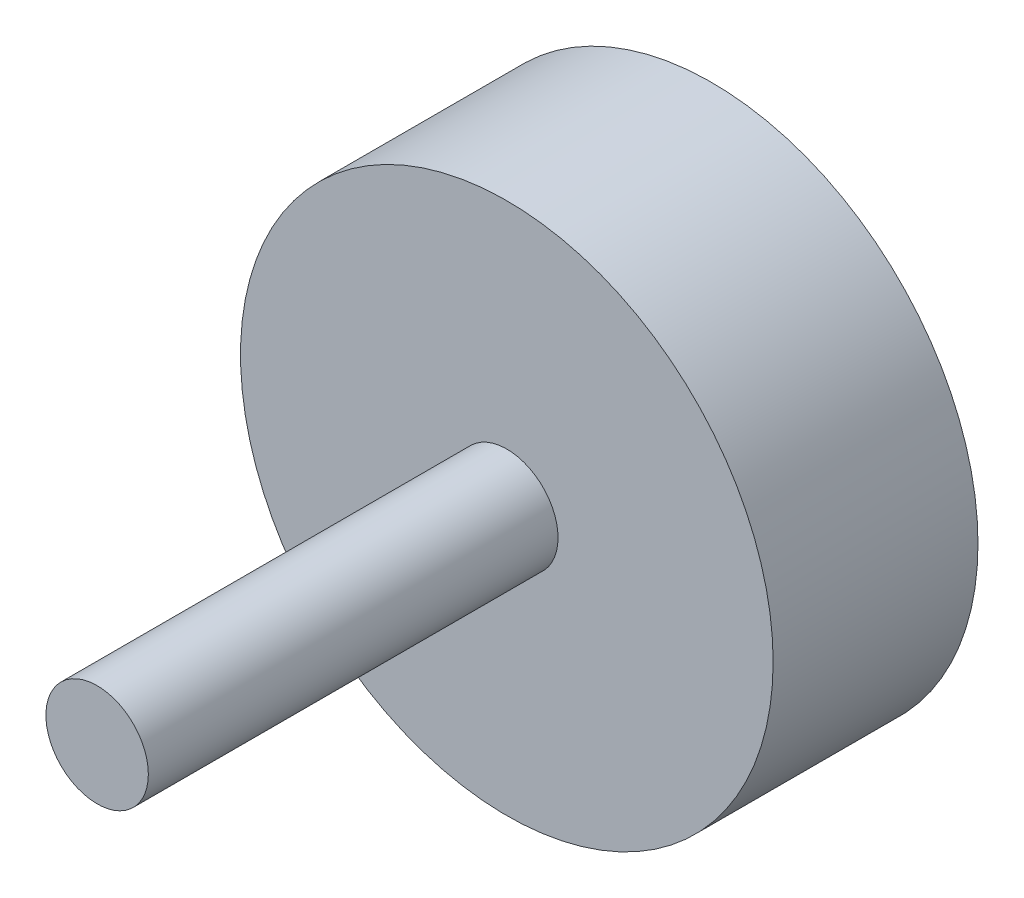
SolidWorks part; units mm, degrees
ref_plane "Front Plane" through (0, 0, 0) normal (0, 0, 1) x (1, 0, 0)
ref_plane "Top Plane" through (0, 0, 0) normal (0, 1, 0) x (1, 0, 0)
ref_plane "Right Plane" through (0, 0, 0) normal (1, 0, 0) x (0, 0, -1)
sketch "Sketch1" plane through (0, 0, 0) normal (0, 0, 1) x (1, 0, 0)
  circle A0 centre (0, 0) radius 26
  dimension "D1" = 52
extrude "Boss-Extrude1" add sketch "Sketch1" along normal blind 20
sketch "Sketch2" plane through (0, 0, 20) normal (0, 0, 1) x (1, 0, 0)
  circle A0 centre (0, 0) radius 5
  dimension "D1" = 10
extrude "Boss-Extrude2" add sketch "Sketch2" along normal blind 40
